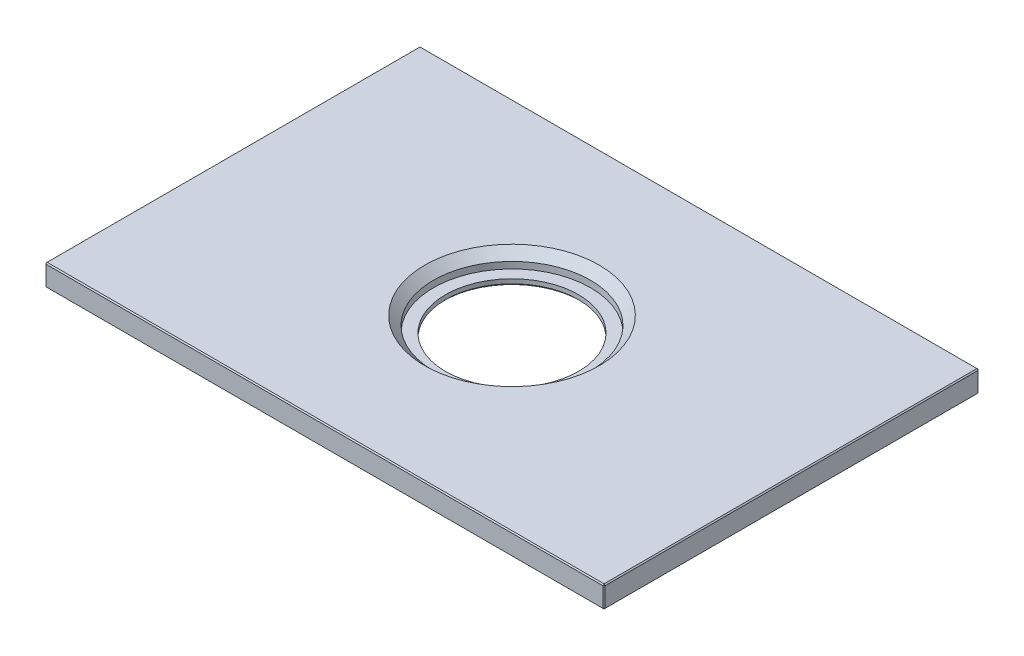
SolidWorks part; units mm, degrees
ref_plane "Front" through (0, 0, 0) normal (0, 0, 1) x (1, 0, 0)
ref_plane "Top" through (0, 0, 0) normal (0, 1, 0) x (1, 0, 0)
ref_plane "Right" through (0, 0, 0) normal (1, 0, 0) x (0, 0, -1)
sketch "Sketch1" plane through (0, 0, 0) normal (0, 1, 0) x (1, 0, 0)
  line L1 (-64.1, -43) -> (64.1, -43)
  line L2 (-64.1, -43) -> (-64.1, 43)
  line L3 (-64.1, 43) -> (64.1, 43)
  line L4 (64.1, -43) -> (64.1, 43)
  line L5 (-64.1, -43) -> (64.1, 43) construction
  line L6 (-64.1, 43) -> (64.1, -43) construction
  point P0 (0, 0)
  dimension "D1" = 128.2
  dimension "D2" = 86
extrude "Extrude1" add sketch "Sketch1" along normal blind 5
sketch "Sketch4" plane through (0, 5, 0) normal (0, 1, 0) x (-1, 0, 0)
  circle A0 centre (0, 0) radius 18
  dimension "D1" = 36
extrude "Extrude4" cut sketch "Sketch4" against normal blind 3.5
sketch "Sketch6" plane through (0, 1.5, 0) normal (0, 1, 0) x (1, 0, 0)
  circle A0 centre (0, 0) radius 15.25
  dimension "D1" = 30.5
extrude "Extrude6" cut sketch "Sketch6" against normal through all
chamfer "Chamfer5" distance 0.5 angle 45 1 edges at (0, 0, 15.25)
chamfer "Chamfer6" distance 2 angle 45 1 edges at (0, 5, 18)
chamfer "Chamfer7" distance 0.25 angle 45 12 edges at (-64.1, 5, 0) (-64.1, 0, 0) (-64.1, 2.5, 43) (0, 5, 43) (0, 0, 43) (64.1, 2.5, 43) (64.1, 5, 0) (64.1, 0, 0) (64.1, 2.5, -43) (0, 5, -43) (-64.1, 2.5, -43) (0, 0, -43)
